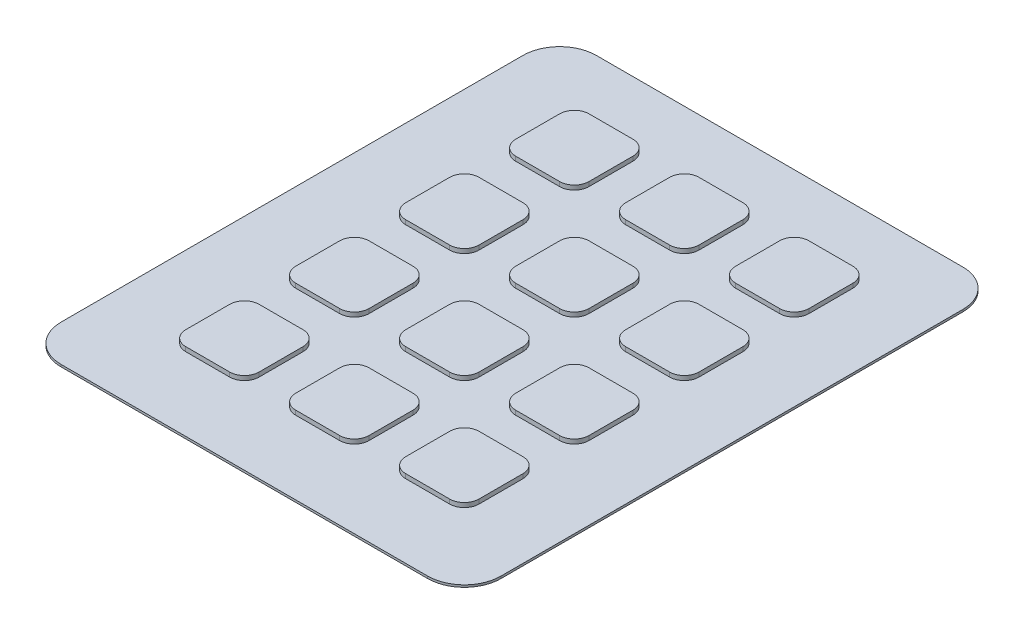
SolidWorks part; units mm, degrees
ref_plane "Front Plane" through (0, 0, 0) normal (0, 0, 1) x (1, 0, 0)
ref_plane "Top Plane" through (0, 0, 0) normal (0, 1, 0) x (1, 0, 0)
ref_plane "Right Plane" through (0, 0, 0) normal (1, 0, 0) x (0, 0, -1)
sketch "Sketch1" plane through (0, 0, 0) normal (0, 1, 0) x (1, 0, 0)
  line L1 (-43.75, 41.8393) -> (16.25, 41.8393)
  line L2 (-43.75, 41.8393) -> (-43.75, -31.1607)
  line L3 (-43.75, -31.1607) -> (16.25, -31.1607)
  line L4 (16.25, 41.8393) -> (16.25, -31.1607)
  dimension "D1" = 73
  dimension "D2" = 60
extrude "Boss-Extrude1" add sketch "Sketch1" along normal blind 0.3
fillet "Fillet1" radius 5 4 edges at (-43.75, 0.15, 31.1607) (-43.75, 0.15, -41.8393) (16.25, 0.15, -41.8393) (16.25, 0.15, 31.1607)
sketch "Sketch2" plane through (0, 0.3, 0) normal (0, 1, 0) x (1, 0, 0)
  line L1 (6.25, -21.1607) -> (-3.75, -21.1607)
  line L2 (6.25, -21.1607) -> (6.25, -11.1607)
  line L3 (6.25, -11.1607) -> (-3.75, -11.1607)
  line L4 (-3.75, -21.1607) -> (-3.75, -11.1607)
  line L5 (16.25, -26.1607) -> (16.25, 36.8393) construction
  dimension "D1" = 10
  dimension "D2" = 10
  dimension "D3" = 10
  dimension "D4" = 10
extrude "Boss-Extrude2" add sketch "Sketch2" along normal blind 0.6
fillet "Fillet2" radius 2 4 edges at (6.25, 0.6, 21.1607) (6.25, 0.6, 11.1607) (-3.75, 0.6, 21.1607) (-3.75, 0.6, 11.1607)
pattern_linear "LPattern1" count 3 spacing 15 along (-1, 0, 0) count 4 spacing 15 along (0, 0, -1) of "Boss-Extrude2", "Fillet2"
